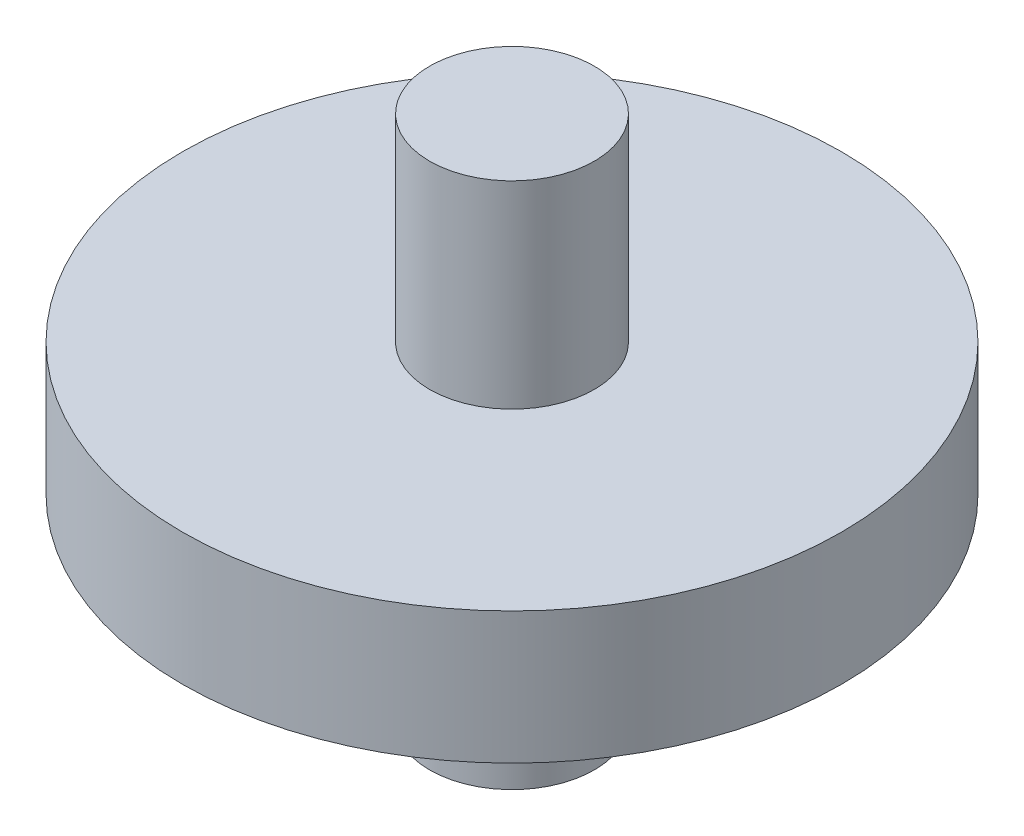
SolidWorks part; units mm, degrees
ref_plane "Plano frontal" through (0, 0, 0) normal (0, 0, 1) x (1, 0, 0)
ref_plane "Plano superior" through (0, 0, 0) normal (0, 1, 0) x (1, 0, 0)
ref_plane "Plano direito" through (0, 0, 0) normal (1, 0, 0) x (0, 0, -1)
sketch "Esboço2" plane through (0, 0, 0) normal (0, 1, 0) x (1, 0, 0)
  circle A0 centre (0, 0) radius 50
  dimension "D1" = 100
extrude "Ressalto-extrusão1" add sketch "Esboço2" along normal blind 20
ref_plane "Plano1" through (0, 10, 0) normal (0, 1, 0) x (1, 0, 0)
sketch "Esboço3" plane through (0, 10, 0) normal (0, 1, 0) x (1, 0, 0)
  circle A0 centre (0, 0) radius 12.5
  dimension "D1" = 25
extrude "Ressalto-extrusão2" add sketch "Esboço3" along normal blind 40 and the other way blind 40
